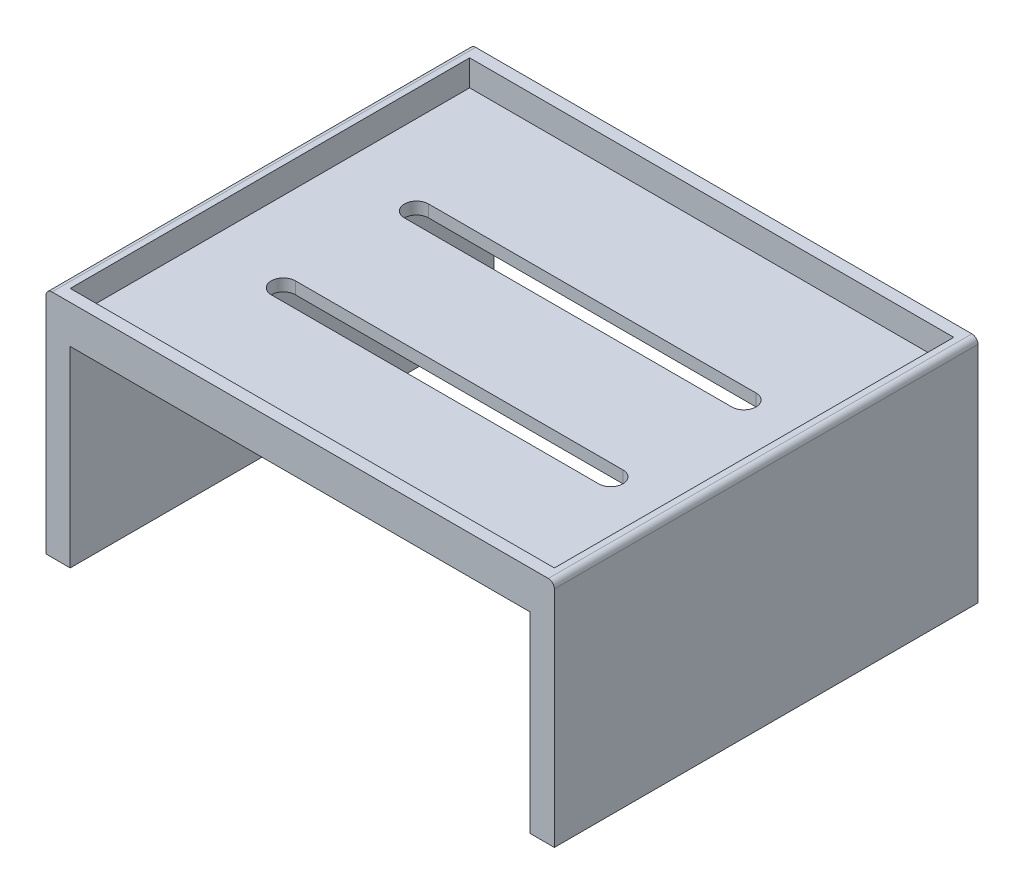
SolidWorks part; units mm, degrees
ref_plane "Front Plane" through (0, 0, 0) normal (0, 0, 1) x (1, 0, 0)
ref_plane "Top Plane" through (0, 0, 0) normal (0, 1, 0) x (1, 0, 0)
ref_plane "Right Plane" through (0, 0, 0) normal (1, 0, 0) x (0, 0, -1)
sketch "Sketch3" plane through (0, 0, 0) normal (0, 0, 1) x (1, 0, 0)
  line L0 (-76.0997, 110.6522) -> (343.9003, 110.6522)
  line L1 (-76.0997, 110.6522) -> (-76.0997, -79.3478)
  line L2 (343.9003, 110.6522) -> (343.9003, -79.3478)
  line L3 (-76.0997, -79.3478) -> (-56.0997, -79.3478)
  line L4 (-56.0997, -79.3478) -> (-56.0997, 79.1522)
  line L5 (343.9003, -79.3478) -> (323.9003, -79.3478)
  line L6 (323.9003, -79.3478) -> (323.9003, 79.1522)
  line L7 (323.9003, 79.1522) -> (-56.0997, 79.1522)
  dimension "D1" = 420
  dimension "D2" = 190
  dimension "D3" = 190
  dimension "D4" = 20
  dimension "D5" = 31.5
  dimension "D6" = 20
extrude "Boss-Extrude1" add sketch "Sketch3" against normal blind 350
sketch "Sketch4" plane through (0, 110.6522, 0) normal (0, 1, 0) x (1, 0, 0)
  line L0 (-76.0997, 0) -> (-76.0997, 350)
  line L1 (-76.0997, 350) -> (343.9003, 350)
  line L2 (343.9003, 350) -> (343.9003, 0)
  line L3 (343.9003, 0) -> (-76.0997, 0)
  line L4 (-76.0997, 340) -> (343.9003, 340)
  line L5 (-76.0997, 10) -> (343.9003, 10)
  line L6 (-66.0997, 340) -> (-66.0997, 10)
  line L7 (333.9003, 340) -> (333.9003, 10)
  dimension "D1" = 10
  dimension "D2" = 10
  dimension "D3" = 10
  dimension "D4" = 10
extrude "Cut-Extrude1" cut sketch "Sketch4" against normal blind 21.5 contours L7 L4 L6 L5
sketch "Sketch5" plane through (0, 89.1522, 0) normal (0, 1, 0) x (1, 0, 0)
  line L0 (-66.0997, 340) -> (-66.0997, 10)
  line L1 (-31.0997, 175) -> (98.9003, 175)
  line L2 (-31.0997, 175) -> (-31.0997, 45)
  line L3 (-31.0997, 45) -> (98.9003, 45)
  line L4 (98.9003, 175) -> (98.9003, 45)
  line L5 (-66.0997, 10) -> (333.9003, 10)
  line L6 (333.9003, 10) -> (333.9003, 340)
  line L7 (333.9003, 340) -> (-66.0997, 340)
  line L8 (-21.0997, 237.5528) -> (88.9003, 237.5528) construction
  line L9 (-21.0997, 247.5528) -> (88.9003, 247.5528)
  line L10 (-21.0997, 227.5528) -> (88.9003, 227.5528)
  line L11 (-21.0997, 305.2666) -> (88.9003, 305.2666) construction
  line L12 (-21.0997, 315.2666) -> (88.9003, 315.2666)
  line L13 (-21.0997, 295.2666) -> (88.9003, 295.2666)
  arc A0 (-21.0997, 247.5528) -> (-21.0997, 227.5528) centre (-21.0997, 237.5528) ccw
  arc A1 (88.9003, 227.5528) -> (88.9003, 247.5528) centre (88.9003, 237.5528) ccw
  arc A2 (-21.0997, 315.2666) -> (-21.0997, 295.2666) centre (-21.0997, 305.2666) ccw
  arc A3 (88.9003, 295.2666) -> (88.9003, 315.2666) centre (88.9003, 305.2666) ccw
  point P14 (33.9003, 237.5528)
  point P19 (-31.0997, 237.5528)
  point P22 (33.9003, 305.2666)
  dimension "D7" = 110
  dimension "D10" = 10
  dimension "D11" = 20
  dimension "D1" = 130
  dimension "D2" = 130
  dimension "D3" = 400
  dimension "D4" = 35
  dimension "D5" = 35
  dimension "D6" = 20
  dimension "D8" = 35
  dimension "D9" = 110
extrude "Cut-Extrude2" cut sketch "Sketch5" against normal blind 30 contours L2 L1 L4 L3 | L10 A1 L9 A0 | L13 A3 L12 A2
sketch "Sketch6" plane through (0, 0, 0) normal (0, 0, 1) x (1, 0, 0)
  line L0 (-76.0997, 100.6522) -> (-76.0997, -77.3478)
  line L1 (-74.0997, -79.3478) -> (-58.0997, -79.3478)
  line L2 (-56.0997, -77.3478) -> (-56.0997, 79.1522)
  line L3 (-56.0997, 79.1522) -> (323.9003, 79.1522)
  line L4 (323.9003, 79.1522) -> (323.9003, -77.3478)
  line L5 (325.9003, -79.3478) -> (341.9003, -79.3478)
  line L6 (343.9003, -77.3478) -> (343.9003, 100.6522)
  line L7 (333.9003, 110.6522) -> (-66.0997, 110.6522)
  line L8 (-76.0997, 110.6522) -> (-76.0997, 100.6522)
  line L9 (-66.0997, 110.6522) -> (-76.0997, 110.6522)
  line L10 (333.9003, 110.6522) -> (343.9003, 110.6522)
  line L11 (343.9003, 110.6522) -> (343.9003, 100.6522)
  line L12 (343.9003, 100.6522) -> (343.9003, 110.6522)
  line L13 (343.9003, -77.3478) -> (343.9003, -79.3478)
  line L14 (343.9003, -79.3478) -> (341.9003, -79.3478)
  line L15 (323.9003, -77.3478) -> (323.9003, -79.3478)
  line L16 (323.9003, -79.3478) -> (325.9003, -79.3478)
  line L17 (-56.0997, -77.3478) -> (-56.0997, -79.3478)
  line L18 (-56.0997, -79.3478) -> (-58.0997, -79.3478)
  line L19 (-74.0997, -79.3478) -> (-76.0997, -79.3478)
  line L20 (-76.0997, -79.3478) -> (-76.0997, -77.3478)
  arc A0 (343.9003, 100.6522) -> (333.9003, 110.6522) centre (333.9003, 100.6522) ccw
  arc A1 (-76.0997, 100.6522) -> (-66.0997, 110.6522) centre (-66.0997, 100.6522) cw
  arc A2 (341.9003, -79.3478) -> (343.9003, -77.3478) centre (341.9003, -77.3478) ccw
  arc A3 (325.9003, -79.3478) -> (323.9003, -77.3478) centre (325.9003, -77.3478) cw
  arc A4 (-58.0997, -79.3478) -> (-56.0997, -77.3478) centre (-58.0997, -77.3478) ccw
  arc A5 (-74.0997, -79.3478) -> (-76.0997, -77.3478) centre (-74.0997, -77.3478) cw
  point P18 (343.9003, 110.6522)
  point P21 (-76.0997, 110.6522)
  point P24 (343.9003, -79.3478)
  point P27 (323.9003, -79.3478)
  point P30 (-56.0997, -79.3478)
  point P33 (-76.0997, -79.3478)
  dimension "D1" = 10
  dimension "D2" = 2
sketch "Sketch9" plane through (0, -79.3478, 0) normal (0, -1, 0) x (1, 0, 0)
  line L1 (343.9003, -350) -> (323.9003, -350)
  line L2 (343.9003, -350) -> (343.9003, 0)
  line L3 (343.9003, 0) -> (323.9003, 0)
  line L4 (323.9003, -350) -> (323.9003, 0)
sketch "Sketch10" plane through (0, -79.3478, 0) normal (0, -1, 0) x (1, 0, 0)
  line L1 (-56.0997, -350) -> (-76.0997, -350)
  line L2 (-56.0997, -350) -> (-56.0997, 0)
  line L3 (-56.0997, 0) -> (-76.0997, 0)
  line L4 (-76.0997, -350) -> (-76.0997, 0)
fillet "Fillet1" radius 5 2 edges at (-76.0997, 110.6522, -175) (343.9003, 110.6522, -175)
sketch "Sketch15" plane through (0, 0, -175) normal (0, 0, 1) x (1, 0, 0)
  line L1 (98.9003, 89.1522) -> (-31.0997, 89.1522)
  line L2 (98.9003, 89.1522) -> (98.9003, 79.1522)
  line L3 (98.9003, 79.1522) -> (-31.0997, 79.1522)
  line L4 (-31.0997, 89.1522) -> (-31.0997, 79.1522)
extrude "Cut-Extrude3" cut sketch "Sketch15" against normal blind 25
sketch "Sketch16" plane through (0, 0, -45) normal (0, 0, -1) x (-1, 0, 0)
  line L1 (-98.9003, 79.1522) -> (31.0997, 79.1522)
  line L2 (-98.9003, 79.1522) -> (-98.9003, 89.1522)
  line L3 (-98.9003, 89.1522) -> (31.0997, 89.1522)
  line L4 (31.0997, 79.1522) -> (31.0997, 89.1522)
extrude "Boss-Extrude6" add sketch "Sketch16" along normal blind 25
sketch "Sketch22" plane through (0, 89.1522, 0) normal (0, 1, 0) x (1, 0, 0)
  line L1 (98.9003, 70) -> (-31.0997, 70)
  line L2 (98.9003, 70) -> (98.9003, 200)
  line L3 (98.9003, 200) -> (-31.0997, 200)
  line L4 (-31.0997, 70) -> (-31.0997, 200)
extrude "Boss-Extrude11" add sketch "Sketch22" against normal blind 10
sketch "Sketch23" plane through (0, 89.1522, 0) normal (0, 1, 0) x (1, 0, 0)
  line L0 (88.9003, 315.2666) -> (-21.0997, 315.2666)
  line L1 (88.9003, 295.2666) -> (-21.0997, 295.2666)
  line L2 (88.9003, 305.2666) -> (-21.0997, 305.2666) construction
  line L3 (88.9003, 295.2666) -> (-21.0997, 295.2666)
  line L4 (88.9003, 315.2666) -> (-21.0997, 315.2666)
  line L5 (88.9003, 247.5528) -> (-21.0997, 247.5528)
  line L6 (-21.0997, 227.5528) -> (88.9003, 227.5528)
  line L7 (-21.0997, 237.5528) -> (88.9003, 237.5528) construction
  line L8 (-21.0997, 247.5528) -> (88.9003, 247.5528)
  line L9 (-21.0997, 227.5528) -> (88.9003, 227.5528)
  arc A0 (88.9003, 295.2666) -> (88.9003, 315.2666) centre (88.9003, 305.2666) ccw
  arc A1 (-21.0997, 315.2666) -> (-21.0997, 295.2666) centre (-21.0997, 305.2666) ccw
  arc A2 (-21.0997, 247.5528) -> (-21.0997, 227.5528) centre (-21.0997, 237.5528) ccw
  arc A3 (88.9003, 227.5528) -> (88.9003, 247.5528) centre (88.9003, 237.5528) ccw
  point P11 (33.9003, 305.2666)
  point P27 (33.9003, 237.5528)
  arc M5 (-21.0997, 227.5528) -> (-21.0997, 247.5528) centre (-21.0997, 237.5528) cw
  line M6 (-21.0997, 247.5528) -> (88.9003, 247.5528)
  arc M7 (88.9003, 247.5528) -> (88.9003, 227.5528) centre (88.9003, 237.5528) cw
  line M8 (88.9003, 227.5528) -> (-21.0997, 227.5528)
  arc M9 (-21.0997, 295.2666) -> (-21.0997, 315.2666) centre (-21.0997, 305.2666) cw
  line M10 (-21.0997, 315.2666) -> (88.9003, 315.2666)
  arc M11 (88.9003, 315.2666) -> (88.9003, 295.2666) centre (88.9003, 305.2666) cw
  line M12 (88.9003, 295.2666) -> (-21.0997, 295.2666)
  dimension "D1" = 20
  dimension "D2" = 20
extrude "Boss-Extrude12" add sketch "Sketch23" against normal blind 10 contours M9 M12 M11 M10 | M5 M8 M7 M6
sketch "Sketch24" plane through (0, 89.1522, 0) normal (0, 1, 0) x (1, 0, 0)
  line L0 (0, 230) -> (270.5188, 230) construction
  line L1 (0, 240) -> (270.5188, 240)
  line L2 (0, 220) -> (270.5188, 220)
  line L3 (270.5188, 120) -> (0, 120) construction
  line L4 (270.5188, 110) -> (0, 110)
  line L5 (270.5188, 130) -> (0, 130)
  arc A0 (0, 240) -> (0, 220) centre (0, 230) ccw
  arc A1 (270.5188, 220) -> (270.5188, 240) centre (270.5188, 230) ccw
  arc A2 (270.5188, 110) -> (270.5188, 130) centre (270.5188, 120) ccw
  arc A3 (0, 130) -> (0, 110) centre (0, 120) ccw
  point P2 (135.2594, 230)
  point P7 (135.2594, 120)
  dimension "D3" = 10
  dimension "D4" = 10
extrude "Cut-Extrude4" cut sketch "Sketch24" against normal blind 10
